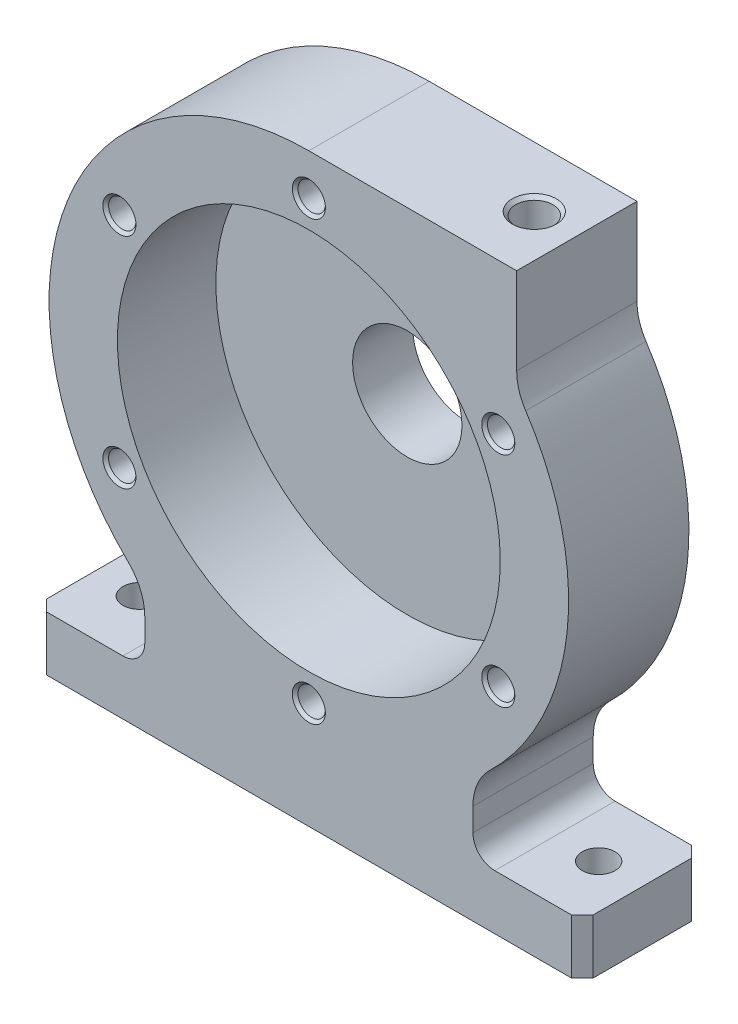
SolidWorks part; units mm, degrees
ref_plane "Front Plane" through (0, 0, 0) normal (0, 0, 1) x (1, 0, 0)
ref_plane "Top Plane" through (0, 0, 0) normal (0, 1, 0) x (1, 0, 0)
ref_plane "Right Plane" through (0, 0, 0) normal (1, 0, 0) x (0, 0, -1)
sketch "Sketch1" plane through (0, 0, 0) normal (0, 0, 1) x (1, 0, 0)
  line L0 (0, 0) -> (0, -59.5) construction
  line L1 (-50, -59.5) -> (50, -59.5)
  line L2 (50, -59.5) -> (50, -49.5)
  line L3 (50, -49.5) -> (34, -49.5)
  line L4 (30, -45.5) -> (30, -41.3068)
  line L5 (0, 47.5) -> (38, 47.5)
  line L6 (38, 47.5) -> (38, 31.6583)
  line L7 (-50, -59.5) -> (-50, -49.5)
  line L8 (-50, -49.5) -> (-34, -49.5)
  line L9 (-30, -45.5) -> (-30, -41.3068)
  arc A0 (0, 47.5) -> (-33.0435, -34.123) centre (0, 0) ccw
  arc A1 (33.0435, -34.123) -> (39.6522, 26.1525) centre (0, 0) ccw
  arc A2 (30, -41.3068) -> (33.0435, -34.123) centre (40, -41.3068) cw
  arc A3 (38, 31.6583) -> (39.6522, 26.1525) centre (48, 31.6583) ccw
  arc A4 (34, -49.5) -> (30, -45.5) centre (34, -45.5) cw
  arc A5 (-34, -49.5) -> (-30, -45.5) centre (-34, -45.5) ccw
  arc A6 (-30, -41.3068) -> (-33.0435, -34.123) centre (-40, -41.3068) ccw
  point P13 (30, -36.8273)
  dimension "D1" = 95
  dimension "D7" = 10
  dimension "D8" = 4
  dimension "D2" = 38
  dimension "D3" = 50
  dimension "D4" = 10
  dimension "D5" = 59.5
  dimension "D6" = 30
extrude "Boss-Extrude1" add sketch "Sketch1" along normal blind 22
sketch "Sketch2" plane through (0, 0, 22) normal (0, 0, 1) x (1, 0, 0)
  circle A0 centre (0, 0) radius 35
  dimension "D1" = 70
extrude "Cut-Extrude1" cut sketch "Sketch2" against normal blind 18
sketch "Sketch3" plane through (0, 0, 0) normal (0, 0, -1) x (-1, 0, 0)
  circle A0 centre (0, 0) radius 14
  dimension "D1" = 28
extrude "Boss-Extrude2" add sketch "Sketch3" along normal blind 7
fillet "Fillet1" radius 4 1 edges at (-14, 0, 0)
sketch "Sketch4" plane through (0, 0, -7) normal (0, 0, -1) x (-1, 0, 0)
  circle A0 centre (0, 0) radius 10
  dimension "D1" = 20
extrude "Cut-Extrude2" cut sketch "Sketch4" against normal through all
chamfer "Chamfer1" distance 2 angle 45 4 edges at (-50, -54.5, 0) (-50, -54.5, 22) (50, -54.5, 0) (50, -54.5, 22)
sketch "Sketch5" plane through (0, 47.5, 0) normal (0, 1, 0) x (1, 0, 0)
  line L0 (38, -11) -> (0, -11) construction
  line L1 (38, -22) -> (38, 0) construction
  line L2 (0, -22) -> (0, 0) construction
hole_wizard "M8x1.25 Tapped Hole1" positions "Sketch6" profile "Sketch7" tap size "M8x1.25" standard "ANSI Metric"
sketch "Sketch6" plane through (0, 47.5, 0) normal (0, 1, 0) x (1, 0, 0)
  line L0 (38, -11) -> (0, -11) construction
  line L1 (38, -22) -> (38, 0) construction
  point P0 (30.2242, -11)
  dimension "D1" = 7.7759
sketch "Sketch7" plane through (30.2242, 47.5, 11) normal (1, 0, 0) x (0, 0, 1)
  line L0 (0, 0) -> (0, 31.7929)
  line L1 (0, 31.7929) -> (3.4, 29.75)
  line L2 (3.4, 29.75) -> (3.4, 0.625)
  line L3 (3.4, 0.625) -> (4.025, 0)
  line L5 (4.025, 0) -> (0, 0)
  line L6 (-3.4, 0.625) -> (-4.025, 0) construction
  line L10 (0, 31.7929) -> (-3.4, 29.75) construction
  line L11 (0, -6.35) -> (0, 107.95) construction
  dimension "Tap Drill Dia." = 6.8
  dimension "Tap Drill Depth" = 29.75
  dimension "Near C'Sink Dia." = 8.05
  dimension "Near C'Sink Angle" = 90
  dimension "Drill Angle" = 118
cosmetic thread "Hole Thread1" parameters "D1"=16, "D2"=8
sketch "Sketch8" plane through (0, 0, 22) normal (0, 0, 1) x (1, 0, 0)
  circle A0 centre (0, 0) radius 40 construction
  dimension "D1" = 80
hole_wizard "M6x1.0 Tapped Hole1" positions "Sketch9" profile "Sketch10" tap size "M6x1.0" standard "ANSI Metric"
sketch "Sketch9" plane through (0, 0, 22) normal (0, 0, 1) x (1, 0, 0)
  circle A0 centre (0, 0) radius 40 construction
  point P0 (0, 40)
sketch "Sketch10" plane through (0, 40, 22) normal (1, 0, 0) x (0, -1, 0)
  line L0 (0, 0) -> (0, 16.5022)
  line L1 (0, 16.5022) -> (2.5, 15)
  line L2 (2.5, 15) -> (2.5, 0.525)
  line L3 (2.5, 0.525) -> (3.025, 0)
  line L5 (3.025, 0) -> (0, 0)
  line L6 (-2.5, 0.525) -> (-3.025, 0) construction
  line L10 (0, 16.5022) -> (-2.5, 15) construction
  line L11 (0, -6.35) -> (0, 107.95) construction
  dimension "Tap Drill Dia." = 5
  dimension "Tap Drill Depth" = 15
  dimension "Near C'Sink Dia." = 6.05
  dimension "Near C'Sink Angle" = 90
  dimension "Drill Angle" = 118
cosmetic thread "Hole Thread2" parameters "D1"=12, "D2"=6
pattern_circular "CirPattern1" count 6 over 360 about axis through (0, 0, 0) along (0, 0, 1) of "M6x1.0 Tapped Hole1"
hole_wizard "CSK for M8 Countersunk Flat Head Screw1" positions "Sketch11" profile "Sketch12" countersink size "M8" standard "ISO"
sketch "Sketch11" plane through (0, -59.5, 0) normal (0, -1, 0) x (-1, 0, 0)
  line L0 (-50, -20) -> (-50, -2) construction
  line L1 (50, -20) -> (50, -2) construction
  point P0 (42, -11)
  point P2 (-42, -11)
  point P9 (0, 0)
  point P10 (50, -11)
  point P11 (-50, -11)
  dimension "D1" = 8
  dimension "D2" = 8
sketch "Sketch12" plane through (-42, -59.5, 11) normal (1, 0, 0) x (0, 0, -1)
  line L0 (0, 0) -> (0, 21.8026)
  line L1 (0, 21.8026) -> (3, 20)
  line L2 (3, 20) -> (3, 1)
  line L3 (3, 1) -> (4, 0)
  line L5 (4, 0) -> (0, 0)
  line L6 (-3, 1) -> (-4, 0) construction
  line L10 (0, 21.8026) -> (-3, 20) construction
  line L11 (0, -6.35) -> (0, 107.95) construction
  dimension "Hole Dia." = 6
  dimension "Hole Depth" = 20
  dimension "Near C'Sink Dia." = 8
  dimension "Near C'Sink Angle" = 90
  dimension "Drill Angle" = 118
